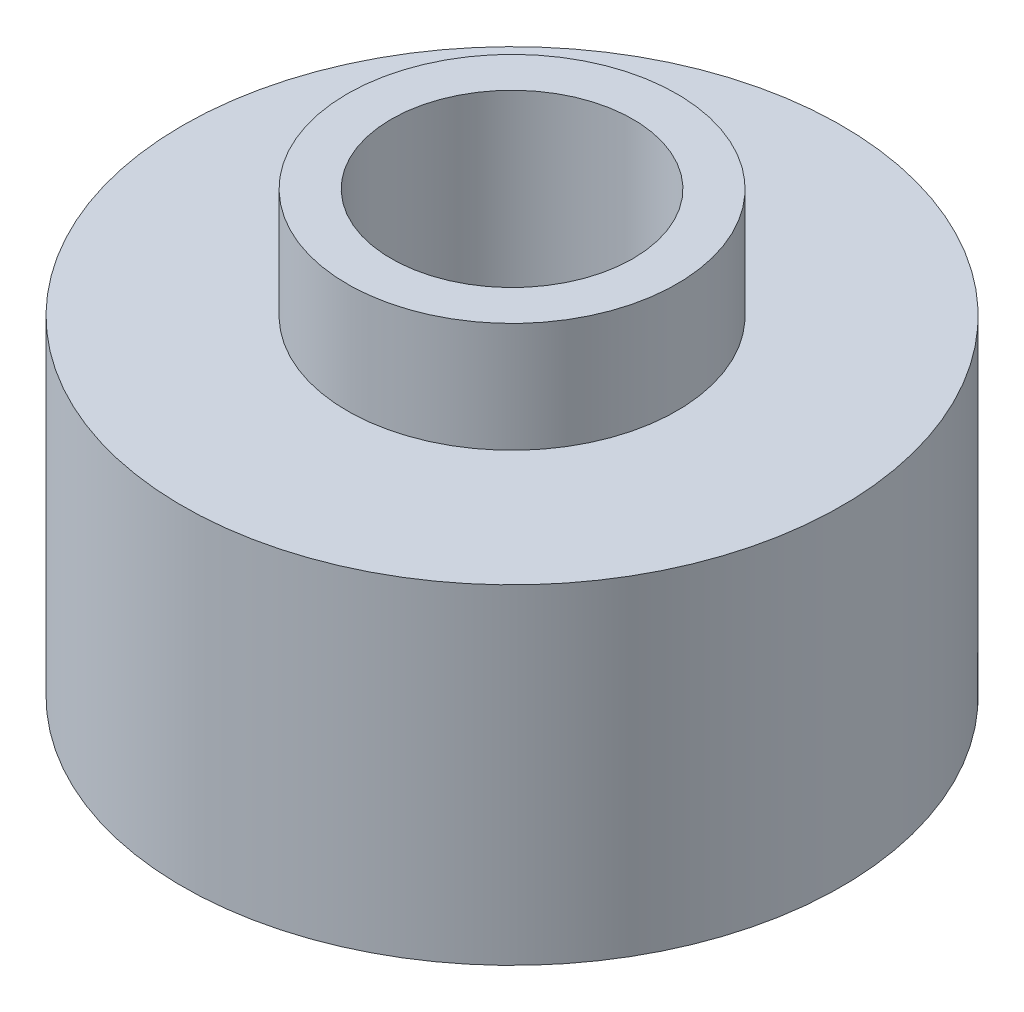
SolidWorks part; units mm, degrees
material "Plain Carbon Steel"
ref_plane "Front Plane" through (0, 0, 0) normal (0, 0, 1) x (1, 0, 0)
ref_plane "Top Plane" through (0, 0, 0) normal (0, 1, 0) x (1, 0, 0)
ref_plane "Right Plane" through (0, 0, 0) normal (1, 0, 0) x (0, 0, -1)
sketch "Sketch1" plane through (0, 0, 0) normal (0, 0, 1) x (1, 0, 0)
  line L0 (0, 0) -> (9.525, 0)
  line L1 (9.525, 0) -> (9.525, 9.525)
  line L2 (9.525, 9.525) -> (4.7625, 9.525)
  line L3 (4.7625, 9.525) -> (4.7625, 12.7)
  line L4 (4.7625, 12.7) -> (0, 12.7)
  line L5 (0, 12.7) -> (0, 0) construction
  line L6 (0, 0) -> (0, 12.7)
  dimension "D1" = 9.525
  dimension "D2" = 9.525
  dimension "D3" = 9.525
  dimension "D4" = 3.175
revolve "Revolve1" add sketch "Sketch1" angle 360 about L5
sketch "Sketch2" plane through (0, 12.7, 0) normal (0, 1, 0) x (1, 0, 0)
  circle A0 centre (0, 0) radius 3.4925
  circle A1 centre (0, 0) radius 4.7625 construction
  dimension "D1" = 1.27
extrude "Cut-Extrude1" cut sketch "Sketch2" against normal through all
